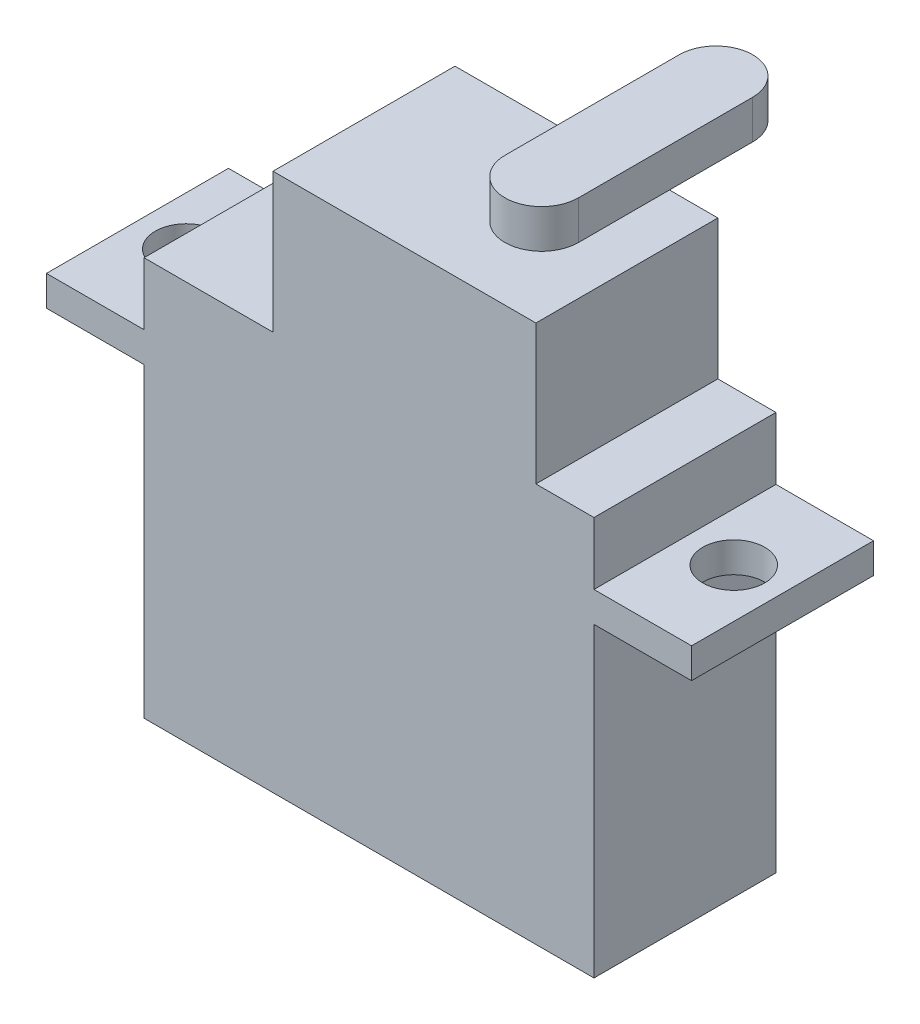
SolidWorks part; units mm, degrees
ref_plane "Front Plane" through (0, 0, 0) normal (0, 0, 1) x (1, 0, 0)
ref_plane "Top Plane" through (0, 0, 0) normal (0, 1, 0) x (1, 0, 0)
ref_plane "Right Plane" through (0, 0, 0) normal (1, 0, 0) x (0, 0, -1)
sketch "Sketch3" plane through (0, 0, 0) normal (0, 1, 0) x (1, 0, 0)
  line L1 (0, 0) -> (29.5148, 0)
  line L2 (0, 0) -> (0, -11.938)
  line L3 (0, -11.938) -> (29.5148, -11.938)
  line L4 (29.5148, 0) -> (29.5148, -11.938)
  dimension "D1" = 11.938
  dimension "D2" = 29.5148
extrude "Boss-Extrude1" add sketch "Sketch3" along normal blind 26.162
sketch "Sketch4" plane through (29.5148, 0, 0) normal (1, 0, 0) x (0, 0, -1)
  line L0 (-11.938, 26.162) -> (-11.938, 0) construction
  line L1 (-11.938, 22.0726) -> (0, 22.0726)
  line L2 (-11.938, 22.0726) -> (-11.938, 20.0914)
  line L3 (-11.938, 20.0914) -> (0, 20.0914)
  line L4 (0, 22.0726) -> (0, 20.0914)
  line L5 (0, 26.162) -> (0, 0) construction
  line L6 (-11.938, 26.162) -> (0, 26.162) construction
  dimension "D1" = 1.9812
  dimension "D2" = 6.0706
extrude "Boss-Extrude2" add sketch "Sketch4" along normal blind 6.4008
ref_plane "Plane1" through (14.7574, 0, 0) normal (1, 0, 0) x (0, 0, -1)
mirror "Mirror1" about plane through (14.7574, 0, 0) normal (1, 0, 0) of "Boss-Extrude2"
sketch "Sketch5" plane through (0, 22.0726, 0) normal (0, 1, 0) x (1, 0, 0)
  line L0 (32.7152, 0) -> (32.7152, -11.938) construction
  line L1 (35.9156, 0) -> (29.5148, 0) construction
  line L2 (35.9156, -11.938) -> (29.5148, -11.938) construction
  circle A0 centre (32.7152, -5.969) radius 2.032
  dimension "D1" = 4.064
extrude "Cut-Extrude1" cut sketch "Sketch5" against normal blind 6.4008
mirror "Mirror2" about plane through (14.7574, 0, 0) normal (1, 0, 0) of "Cut-Extrude1"
sketch "Sketch6" plane through (0, 26.162, 0) normal (0, 1, 0) x (1, 0, 0)
  line L0 (29.5148, 0) -> (0, 0) construction
  line L1 (8.4582, 0) -> (25.7048, 0)
  line L2 (8.4582, 0) -> (8.4582, -11.938)
  line L3 (8.4582, -11.938) -> (25.7048, -11.938)
  line L4 (25.7048, 0) -> (25.7048, -11.938)
  line L5 (0, -11.938) -> (29.5148, -11.938) construction
  line L6 (29.5148, -11.938) -> (29.5148, 0) construction
  dimension "D1" = 3.81
  dimension "D2" = 17.2466
extrude "Boss-Extrude3" add sketch "Sketch6" along normal blind 9.144
sketch "Sketch7" plane through (0, 35.306, 0) normal (0, 1, 0) x (1, 0, 0)
  line L0 (25.7048, -5.969) -> (8.4582, -5.969) construction
  line L1 (25.7048, -11.938) -> (25.7048, 0) construction
  line L2 (8.4582, 0) -> (8.4582, -11.938) construction
  line L3 (29.5148, 0) -> (29.5148, -11.938) construction
  line L4 (20.1168, -5.969) -> (20.1168, 5.461) construction
  line L5 (17.7038, -5.969) -> (17.7038, 5.461)
  line L6 (22.5298, -5.969) -> (22.5298, 5.461)
  circle A0 centre (20.1168, -5.969) radius 1.27 construction
  arc A1 (17.7038, -5.969) -> (22.5298, -5.969) centre (20.1168, -5.969) ccw
  arc A2 (22.5298, 5.461) -> (17.7038, 5.461) centre (20.1168, 5.461) ccw
  point P10 (20.1168, -0.254)
  point P16 (20.1168, 7.874)
  dimension "D2" = 2.54
  dimension "D3" = 13.843
  dimension "D1" = 9.398
  dimension "D4" = 4.826
extrude "Boss-Extrude4" add sketch "Sketch7" along normal blind 2.54
